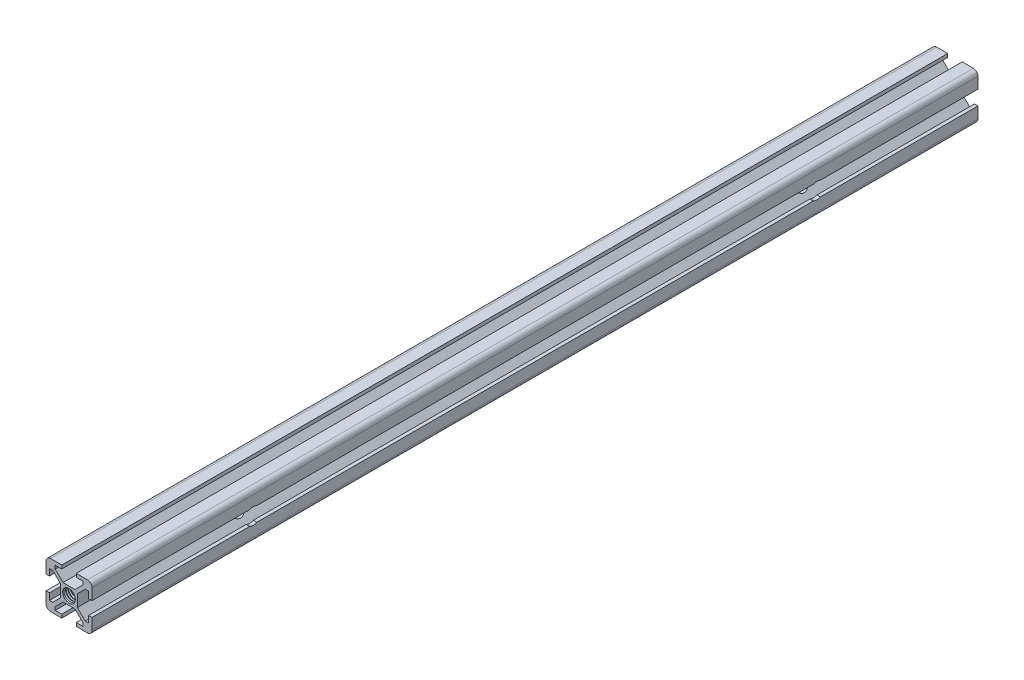
SolidWorks part; units mm, degrees
material "1060 Alloy"
ref_plane "Front Plane" through (0, 0, 0) normal (0, 0, 1) x (1, 0, 0)
ref_plane "Top Plane" through (0, 0, 0) normal (0, 1, 0) x (1, 0, 0)
ref_plane "Right Plane" through (0, 0, 0) normal (1, 0, 0) x (0, 0, -1)
sketch "Sketch1" plane through (0, 0, 0) normal (0, 0, 1) x (1, 0, 0)
  line L0 (0, 0) -> (3.66, 3.66) construction
  line L1 (-2.5993, -3.66) -> (2.5993, -3.66)
  line L2 (-3.66, -2.5993) -> (-3.66, 2.5993)
  line L3 (-2.5993, 3.66) -> (2.5993, 3.66)
  line L4 (3.66, -2.5993) -> (3.66, 2.5993)
  line L5 (-3.66, -3.66) -> (3.66, 3.66) construction
  line L6 (-3.66, 3.66) -> (3.66, -3.66) construction
  line L7 (-8, -10) -> (-3.15, -10)
  line L8 (-10, -8) -> (-10, -3.15)
  line L9 (-8, 10) -> (-3.15, 10)
  line L10 (10, -8) -> (10, -3.15)
  line L11 (-10, -10) -> (3.66, 3.66) construction
  line L12 (-10, 10) -> (9.4142, -9.4142) construction
  line L13 (0.5303, -0.5303) -> (1.0607, 0) construction
  line L14 (-0.5303, 0.5303) -> (0, 1.0607) construction
  line L15 (-0.5303, 0.5303) -> (9.4697, 10.5303) construction
  line L16 (0.5303, -0.5303) -> (10.5303, 9.4697) construction
  line L17 (0, 0) -> (10, 0) construction
  line L18 (-10, -3.15) -> (-8.5, -3.15)
  line L19 (8.5, 3.15) -> (8.5, 5.995)
  line L20 (10, 3.15) -> (10, 8)
  line L21 (8.5, 5.995) -> (7.0557, 5.995)
  line L22 (9.4142, 9.4142) -> (10, 10) construction
  line L23 (0, 0) -> (10, 10) construction
  line L24 (9.4142, 9.4142) -> (10, 10) construction
  line L25 (0, 14.5751) -> (0, -10) construction
  line L26 (0, 0) -> (11.8172, 11.8172) construction
  line L27 (3.15, 10) -> (8, 10)
  line L28 (5.995, 8.5) -> (5.995, 7.0557)
  line L29 (10, 3.15) -> (8.5, 3.15)
  line L30 (3.15, 8.5) -> (5.995, 8.5)
  line L31 (9.8413, 8.7807) -> (10, 8.9393)
  line L32 (8.7807, 9.8413) -> (8.9393, 10)
  line L33 (0.5303, 0.5303) -> (1.0607, 0) construction
  line L34 (-0.5303, -0.5303) -> (0, -1.0607) construction
  line L35 (5.995, -8.5) -> (5.995, -7.0557)
  line L36 (3.15, -8.5) -> (5.995, -8.5)
  line L38 (-8, -10) -> (-3.15, -10)
  line L39 (8.5, -5.995) -> (7.0557, -5.995)
  line L40 (8.5, -3.15) -> (8.5, -5.995)
  line L42 (10, -3.15) -> (10, -8)
  line L43 (-8.5, -5.995) -> (-7.0557, -5.995)
  line L44 (-8.5, -3.15) -> (-8.5, -5.995)
  line L45 (-10, 3.15) -> (-8.5, 3.15)
  line L46 (-10, -8) -> (-10, -3.15)
  line L47 (8, -10) -> (3.15, -10)
  line L48 (10, -3.15) -> (8.5, -3.15)
  line L49 (-3.15, -8.5) -> (-5.995, -8.5)
  line L50 (-0.5303, 0.5303) -> (-1.0607, 0) construction
  line L51 (0.5303, -0.5303) -> (0, -1.0607) construction
  line L52 (-5.995, -8.5) -> (-5.995, -7.0557)
  line L53 (-10, 3.15) -> (-10, 8)
  line L54 (3.15, -10) -> (3.15, -8.5)
  line L55 (-8.5, 5.995) -> (-7.0557, 5.995)
  line L56 (-8.5, 3.15) -> (-8.5, 5.995)
  line L57 (-0.5303, -0.5303) -> (-1.0607, 0) construction
  line L58 (0.5303, 0.5303) -> (0, 1.0607) construction
  line L59 (-5.995, 8.5) -> (-5.995, 7.0557)
  line L60 (-3.15, 8.5) -> (-5.995, 8.5)
  line L61 (-3.15, -10) -> (-3.15, -8.5)
  line L62 (8, 10) -> (3.15, 10)
  line L63 (-10, 3.15) -> (-10, 8)
  line L64 (3.15, -10) -> (8, -10)
  line L65 (3.15, -10) -> (8, -10)
  line L66 (-3.15, -10) -> (-8, -10)
  line L67 (-2.5993, 3.66) -> (-5.995, 7.0557)
  line L68 (-3.66, 2.5993) -> (-7.0557, 5.995)
  line L69 (-3.66, -2.5993) -> (-7.0557, -5.995)
  line L70 (-2.5993, -3.66) -> (-5.995, -7.0557)
  line L71 (2.5993, -3.66) -> (5.995, -7.0557)
  line L72 (3.66, -2.5993) -> (7.0557, -5.995)
  line L73 (3.66, 2.5993) -> (7.0557, 5.995)
  line L74 (2.5993, 3.66) -> (5.995, 7.0557)
  line L75 (3.15, 10) -> (8, 10)
  line L76 (-3.15, 10) -> (-8, 10)
  line L78 (3.15, 10) -> (3.15, 8.5)
  line L79 (-3.15, 10) -> (-3.15, 8.5)
  circle A0 centre (0, 0) radius 2.75
  arc A1 (8, 10) -> (10, 8) centre (8, 8) cw
  arc A2 (8, -10) -> (10, -8) centre (8, -8) ccw
  arc A3 (-8, -10) -> (-10, -8) centre (-8, -8) cw
  arc A4 (-8, 10) -> (-10, 8) centre (-8, 8) ccw
  dimension "D1" = 5.5
  dimension "D6" = 2
  dimension "D2" = 7.32
  dimension "D3" = 20
  dimension "D7" = 2.845
  dimension "D9" = 20
  dimension "D12" = 1.4443
  dimension "D13" = 7.32
  dimension "D14" = 3.66
  dimension "D4" = 3.15
  dimension "D5" = 1.5
  dimension "D15" = 4.85
  dimension "D16" = 5.1987
  dimension "D17" = 3.66
  dimension "D18" = 2.845
  dimension "D19" = 6.3
extrude "Boss-Extrude1" add sketch "Sketch1" along normal blind 385 contours L9 A4 L53 L45 L56 L55 L68 L2 L69 L43 L44 L18 L8 A3 L7 L61 L49 L52 L70 L1 L71 L35 L36 L54 L47 A2 L10 L48 L40 L39 L72 L4 L73 L21 L19 L29 L20 A1 L27 L78 L30 L28 L74 L3 L67 L59 L60 L79
ref_plane "Plane1" through (0, 0, 1) normal (0, 0, -1) x (-1, 0, 0)
sketch "Sketch2" plane through (0, 0, 1) normal (0, 0, -1) x (-1, 0, 0)
  circle A0 centre (0, 0) radius 2.15
curve "Helix/Spiral1" pitch 1 height 18.5 turns 18.5
sketch "Sketch3" plane through (0, 0, 0) normal (1, 0, 0) x (0, 0, -1)
  line L0 (-2.2297, 2.75) -> (-0.65, 2.75) construction
  line L1 (0, 2.75) -> (-385, 2.75) construction
  line L2 (-0.65, 3.3895) -> (-1.025, 2.74)
  line L3 (-1.025, 2.74) -> (-0.275, 2.74)
  line L4 (-0.275, 2.74) -> (-0.65, 3.3895)
  line L5 (0, -2.5993) -> (0, 2.5993) construction
  circle A0 centre (-0.65, 2.9565) radius 0.2165 construction
  dimension "D1" = 0.75
  dimension "D2" = 0.65
  dimension "D3" = 0.01
  dimension "D4" = 0
sweep "Cut-Sweep2" cut profiles "Sketch3" path "Helix/Spiral1"
ref_plane "Plane2" through (0, 0, 192.5) normal (0, 0, -1) x (-1, 0, 0)
mirror "Mirror1" about plane through (0, 0, 192.5) normal (0, 0, -1) of "Cut-Sweep2"
sketch "Sketch4" plane through (-10, 0, 0) normal (-1, 0, 0) x (0, 0, 1)
  line L0 (384.9692, 0) -> (0.0308, 0) construction
  circle A0 centre (70.0308, 0) radius 3.5
  circle A1 centre (314.9692, 0) radius 3.5
  dimension "D1" = 7
  dimension "D2" = 70
  dimension "D3" = 70
extrude "Cut-Extrude1" cut sketch "Sketch4" against normal through all
